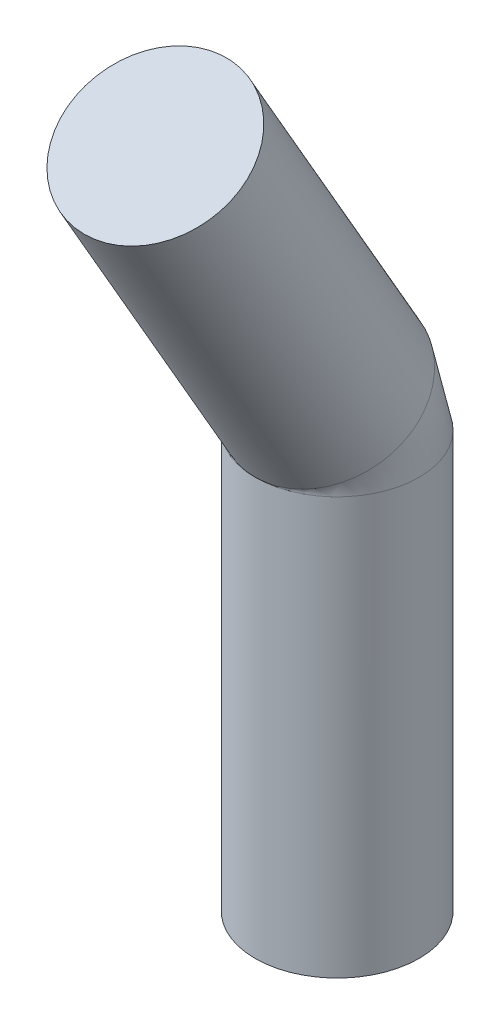
SolidWorks part; units mm, degrees
ref_plane "Front Plane" through (0, 0, 0) normal (0, 0, 1) x (1, 0, 0)
ref_plane "Top Plane" through (0, 0, 0) normal (0, 1, 0) x (1, 0, 0)
ref_plane "Right Plane" through (0, 0, 0) normal (1, 0, 0) x (0, 0, -1)
sketch "Sketch23" plane through (0, 0, 0) normal (0, 1, 0) x (1, 0, 0)
  circle A0 centre (0, 0) radius 0.6
  dimension "D1" = 1.2
sketch "Sketch24" plane through (0, 0, 0) normal (1, 0, 0) x (0, 0, -1)
  line L0 (0, 0) -> (0, 0.5)
  line L1 (0, 55) -> (0, -55) construction
  line L2 (-0.0804, 0.8) -> (-1.3304, 2.9651)
  arc A0 (0, 0.5) -> (-0.0804, 0.8) centre (-0.6, 0.5) ccw
  dimension "D1" = 0.5
  dimension "D2" = 0.6
  dimension "D3" = 30
  dimension "D4" = 2.5
sweep "Sweep4" add profiles "Sketch23" path "Sketch24"
sketch "Sketch25" plane through (0, 0, 0) normal (0, -1, 0) x (-1, 0, 0)
  circle A0 centre (0, 0) radius 0.6
  dimension "D1" = 1.2
extrude "Boss-Extrude2" add sketch "Sketch25" along normal blind 2.55
sketch "Sketch28" plane through (0, 2.7999, 1.6165) normal (0, 0.866, 0.5) x (1, 0, 0)
  line L0 (0, 0.3304) -> (0.6, 0.3304)
  circle A0 centre (0, 0.3304) radius 0.6 construction
